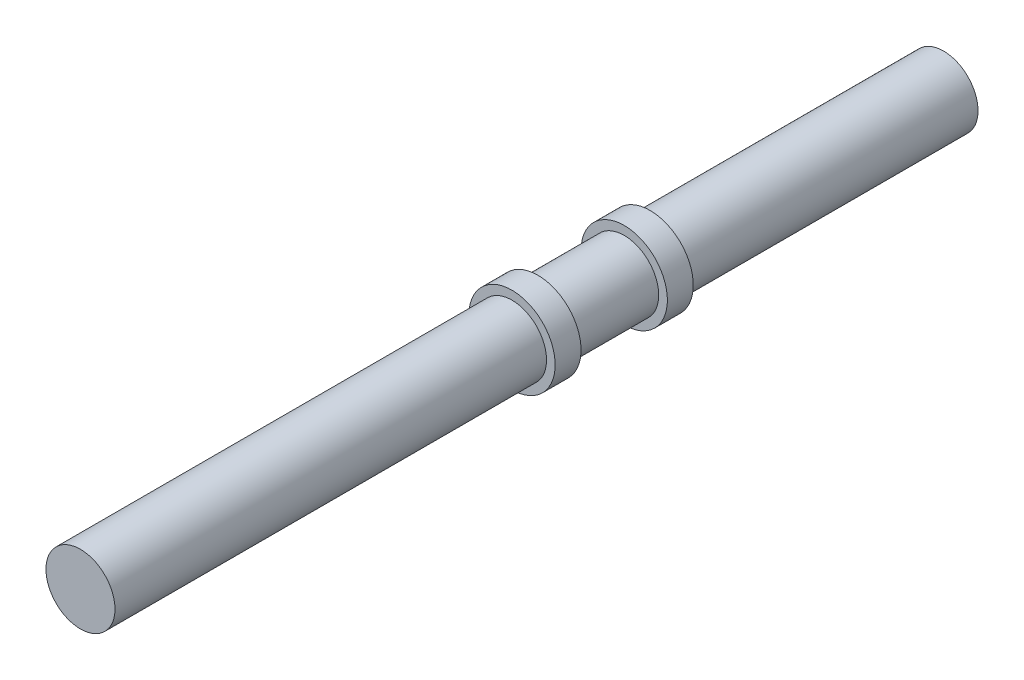
SolidWorks part; units mm, degrees
ref_plane "Front Plane" through (0, 0, 0) normal (0, 0, 1) x (1, 0, 0)
ref_plane "Top Plane" through (0, 0, 0) normal (0, 1, 0) x (1, 0, 0)
ref_plane "Right Plane" through (0, 0, 0) normal (1, 0, 0) x (0, 0, -1)
sketch "Sketch1" plane through (0, 0, 0) normal (0, 0, 1) x (1, 0, 0)
  circle A0 centre (0, 0) radius 4
  dimension "D1" = 8
extrude "Boss-Extrude1" add sketch "Sketch1" along normal blind 50
sketch "Sketch2" plane through (0, 0, 0) normal (0, 0, -1) x (-1, 0, 0)
  circle A0 centre (0, 0) radius 5
extrude "Boss-Extrude2" add sketch "Sketch2" along normal blind 3
sketch "Sketch3" plane through (0, 0, -3) normal (0, 0, -1) x (-1, 0, 0)
  circle A0 centre (0, 0) radius 4
extrude "Boss-Extrude3" add sketch "Sketch3" along normal blind 10
sketch "Sketch4" plane through (0, 0, -13) normal (0, 0, -1) x (-1, 0, 0)
  circle A0 centre (0, 0) radius 5
extrude "Boss-Extrude4" add sketch "Sketch4" along normal blind 3
sketch "Sketch5" plane through (0, 0, -16) normal (0, 0, -1) x (-1, 0, 0)
  circle A0 centre (0, 0) radius 4
extrude "Boss-Extrude5" add sketch "Sketch5" along normal blind 34
